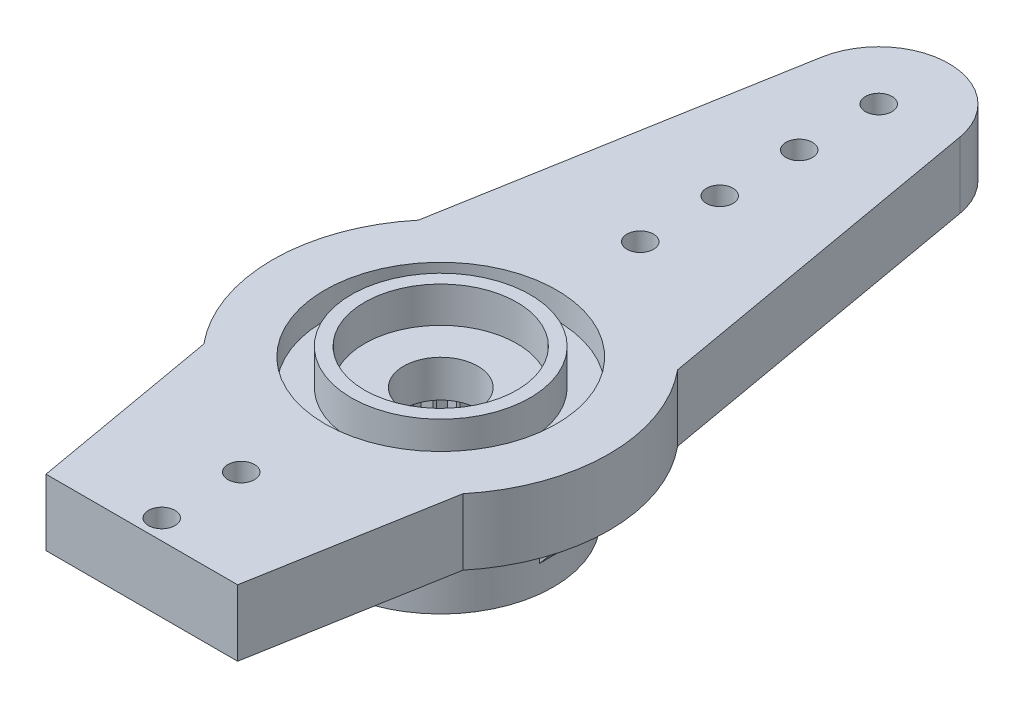
SolidWorks part; units mm, degrees
material "Polyethylene Cross-Linked"
ref_plane "Front Plane" through (0, 0, 0) normal (0, 0, 1) x (1, 0, 0)
ref_plane "Top Plane" through (0, 0, 0) normal (0, 1, 0) x (1, 0, 0)
ref_plane "Right Plane" through (0, 0, 0) normal (1, 0, 0) x (0, 0, -1)
sketch "Sketch1" plane through (0, 0, 0) normal (0, 1, 0) x (1, 0, 0)
  circle A0 centre (0, 0) radius 6.35
  dimension "D1" = 12.7
extrude "Boss-Extrude1" add sketch "Sketch1" along normal blind 5.4
sketch "Sketch2" plane through (0, 5.4, 0) normal (0, 1, 0) x (1, 0, 0)
  line L0 (0, 0) -> (0, 16.53) construction
  line L1 (-2.6097, 16.9902) -> (-4.8916, 4.049)
  line L2 (0, 19.18) -> (0, 16.53) construction
  line L3 (2.6097, 16.9902) -> (4.8916, 4.049)
  arc A0 (2.6097, 16.9902) -> (-2.6097, 16.9902) centre (0, 16.53) ccw
  arc A4 (4.8916, 4.049) -> (-4.8916, 4.049) centre (0, 0) ccw
  circle A5 centre (0, 0) radius 6.35 construction
  dimension "D1" = 5.3
  dimension "D2" = 19.18
  dimension "D3" = 10
  dimension "D4" = 9.7832
extrude "horn" add sketch "Sketch2" against normal blind 2.5
sketch "Sketch4" plane through (0, 5.4, 0) normal (0, -1, 0) x (-1, 0, 0)
  circle A0 centre (0, 0) radius 1.4
  dimension "D1" = 2.8
extrude "Cut-Extrude1" cut sketch "Sketch4" along normal through all
sketch "Sketch5" plane through (0, 0, 0) normal (0, -1, 0) x (-1, 0, 0)
  circle A0 centre (0, 16.53) radius 0.5
  dimension "D1" = 1
extrude "Cut-Extrude2" cut sketch "Sketch5" against normal through all
sketch "Sketch6" plane through (0, 0, 0) normal (0, 1, 0) x (1, 0, 0)
  line L0 (0, 0) -> (0, 16.53) construction
pattern_linear "LPattern1" count 4 spacing 3 along (0, 0, 1) of "Cut-Extrude2"
mirror "Mirror1" about plane through (0, 0, 0) normal (0, 0, 1) of "horn", "LPattern1", "Cut-Extrude2"
sketch "Sketch8" plane through (0, 0, 0) normal (0, -1, 0) x (-1, 0, 0)
  line L0 (0, -2.9) -> (0.2629, -2.5867)
  line L1 (0, -2.9) -> (-0.2629, -2.5867)
  line L2 (0, -2.6) -> (0, -2.9) construction
  line L3 (0, 0) -> (0, -2.6) construction
  arc A1 (-0.2629, -2.5867) -> (0.2629, -2.5867) centre (0, 0) ccw
  dimension "D1" = 0.3
  dimension "D2" = 5.2
  dimension "D3" = 80
extrude "Cut-Extrude4" cut sketch "Sketch8" against normal blind 3
pattern_circular "CirPattern2" count 26 over 360 about axis through (0, 0, 0) along (0, 1, 0) of "Cut-Extrude4"
sketch "Sketch9" plane through (0, 0, 0) normal (0, -1, 0) x (-1, 0, 0)
  circle A0 centre (0, 0) radius 2.6
  arc A1 (-0.2629, -2.5867) -> (0.2629, -2.5867) centre (0, 0) ccw construction
extrude "Cut-Extrude5" cut sketch "Sketch9" against normal blind 3
sketch "Sketch10" plane through (0, 0, 0) normal (0, -1, 0) x (-1, 0, 0)
  circle A0 centre (0, 0) radius 6.35
  circle A1 centre (0, 0) radius 4.25
  circle A2 centre (0, 0) radius 6.35 construction
  dimension "D1" = 8.5
extrude "Cut-Extrude6" cut sketch "Sketch10" against normal up to surface (2.9 mm away) up to face at (0, 2.9, 11.03)
sketch "Sketch11" plane through (0, 0, 0) normal (0, 0, 1) x (1, 0, 0)
  line L2 (4.21, 0.99) -> (5.8127, 2.9)
  line L3 (4.8916, 2.9) -> (6.35, 2.9) construction
  line L4 (5.8127, 2.9) -> (4.21, 2.9)
  line L7 (4.21, 0.99) -> (4.16, 0.99)
  line L8 (4.16, 0.99) -> (4.16, 2.9)
  line L10 (4.21, 0.99) -> (4.21, 2.9) construction
  line L12 (4.16, 2.9) -> (4.21, 2.9)
  line L13 (0, 2.9) -> (4.16, 2.9) construction
  line L14 (-4.25, 2.9) -> (4.25, 2.9) construction
  dimension "D1" = 1.91
  dimension "D2" = 0.05
  dimension "D3" = 40
  dimension "D4" = 4.16
extrude "Boss-Extrude5" add sketch "Sketch11" along normal mid plane 1
pattern_circular "CirPattern3" count 4 over 360 about axis through (0, 0, 0) along (0, 1, 0) of "Boss-Extrude5"
sketch "Sketch12" plane through (0, 5.4, 0) normal (0, 1, 0) x (1, 0, 0)
  circle A0 centre (0, 0) radius 4.375
  dimension "D1" = 8.75
extrude "Cut-Extrude7" cut sketch "Sketch12" against normal blind 1
sketch "Sketch13" plane through (0, 4.4, 0) normal (0, 1, 0) x (1, 0, 0)
  circle A0 centre (0, 0) radius 2.875
  circle A1 centre (0, 0) radius 3.375
  dimension "D1" = 0.5
  dimension "D2" = 6.75
extrude "Boss-Extrude6" add sketch "Sketch13" along normal up to surface (1 mm away)
sketch "Sketch14" plane through (0, 5.4, 0) normal (0, 1, 0) x (1, 0, 0)
  circle A0 centre (0, 0) radius 2.875
  circle A1 centre (0, 0) radius 2.875 construction
  circle A2 centre (0, 0) radius 3.375
  circle A3 centre (0, 0) radius 3.375 construction
extrude "Boss-Extrude7" add sketch "Sketch14" along normal blind 0.35
sketch "Sketch15" plane through (0, 5.4, 0) normal (0, 1, 0) x (1, 0, 0)
  line L0 (-3.6164, -11.2813) -> (3.6164, -11.2813)
  line L1 (-2.6097, -16.9902) -> (-4.8916, -4.049) construction
  line L2 (4.8916, -4.049) -> (2.6097, -16.9902) construction
  line L3 (3.6164, -11.2813) -> (9.3215, -16.3886)
  line L4 (9.3215, -16.3886) -> (4.6607, -20.8467)
  line L5 (4.6607, -20.8467) -> (-5.7753, -20.8467)
  line L6 (-5.7753, -20.8467) -> (-10.6801, -15.719)
  line L7 (-10.6801, -15.719) -> (-9.7336, -14.8137)
  line L8 (-3.6164, -11.2813) -> (-9.7336, -14.8137)
extrude "Cut-Extrude8" cut sketch "Sketch15" against normal through all
